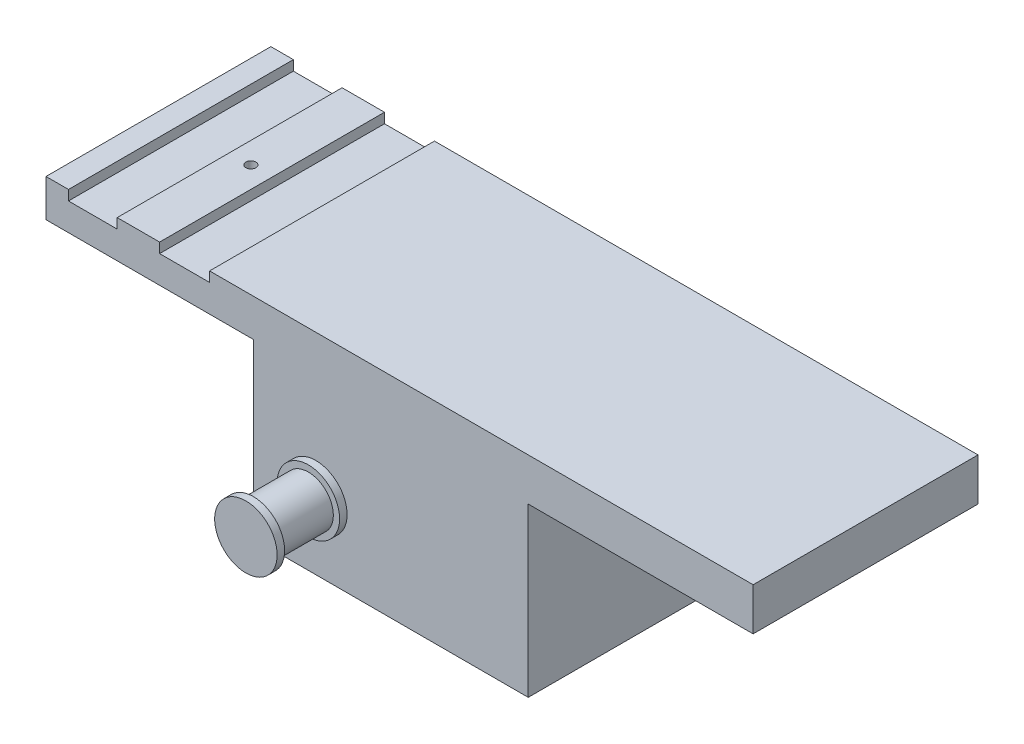
SolidWorks part; units mm, degrees
material "Alloy Steel (SS)"
ref_plane "Front Plane" through (0, 0, 0) normal (0, 0, 1) x (1, 0, 0)
ref_plane "Top Plane" through (0, 0, 0) normal (0, 1, 0) x (1, 0, 0)
ref_plane "Right Plane" through (0, 0, 0) normal (1, 0, 0) x (0, 0, -1)
sketch "Sketch1" plane through (0, 0, 0) normal (0, 0, 1) x (1, 0, 0)
  line L0 (-283, 0) -> (0, 0)
  line L1 (0, 0) -> (0, 15)
  line L2 (0, 15) -> (-217.53, 15)
  line L3 (-217.53, 15) -> (-217.53, 11)
  line L4 (-217.53, 11) -> (-237.53, 11)
  line L5 (-237.53, 11) -> (-237.53, 15)
  line L6 (-237.53, 15) -> (-254.5, 15)
  line L7 (-254.5, 15) -> (-254.5, 11)
  line L8 (-254.5, 11) -> (-274, 11)
  line L9 (-274, 11) -> (-274, 15)
  line L10 (-274, 15) -> (-283, 15)
  line L11 (-283, 15) -> (-283, 0)
  dimension "D1" = 283
  dimension "D2" = 217.53
  dimension "D3" = 9
  dimension "D4" = 19.5
  dimension "D5" = 16.97
  dimension "D6" = 20
  dimension "D7" = 15
  dimension "D8" = 4
extrude "Boss-Extrude1" add sketch "Sketch1" along normal blind 90
sketch "Sketch2" plane through (0, 15, 0) normal (0, 1, 0) x (1, 0, 0)
  line L0 (-283, -45) -> (-71.3341, -45) construction
  line L1 (-283, -90) -> (-283, 0) construction
  line L2 (-246.015, 0) -> (-246.015, -93.7366) construction
  line L3 (-237.53, 0) -> (-254.5, 0) construction
  circle A0 centre (-246.015, -45) radius 2
  dimension "D1" = 4
extrude "Cut-Extrude1" cut sketch "Sketch2" against normal blind 26
sketch "Sketch3" plane through (0, 0, 0) normal (0, 0, -1) x (-1, 0, 0)
  line L0 (213, -0.0192) -> (213, -74.1) construction
  line L1 (213, -74.1) -> (-6.6499, -74.1) construction
  line L2 (283, 0) -> (0, 0) construction
  line L3 (0, 0) -> (0, 15) construction
  line L4 (0, 0) -> (0, -61.6)
  line L5 (180, -61.6) -> (200, -61.6) construction
  line L6 (200, -61.6) -> (200, 7.5)
  line L7 (136.6106, -45.6) -> (183.3894, -45.6)
  line L8 (183.3894, -45.6) -> (191.9233, -69.0468)
  line L9 (160, -61.6) -> (160, -80.8536) construction
  line L10 (136.6106, -45.6) -> (128.0767, -69.0468)
  line L11 (140, -61.6) -> (60, -61.6) construction
  line L12 (0, -61.6) -> (200, -61.6) construction
  line L13 (100, -61.6) -> (100, 5.3066) construction
  line L14 (16.6106, -45.6) -> (8.0767, -69.0468)
  line L15 (63.3894, -45.6) -> (16.6106, -45.6)
  line L16 (63.3894, -45.6) -> (71.9233, -69.0468)
  line L17 (20, -61.6) -> (0, -61.6) construction
  line L18 (0, 0) -> (0, 7.5)
  line L19 (0, 7.5) -> (200, 7.5)
  line L20 (0, -69.0468) -> (8.0767, -69.0468)
  line L21 (200, -69.0468) -> (200, -61.6)
  line L22 (0, -61.6) -> (0, -69.0468)
  line L24 (71.9233, -69.0468) -> (128.0767, -69.0468)
  line L25 (191.9233, -69.0468) -> (200, -69.0468)
  circle A0 centre (160, -61.6) radius 10.5 construction
  circle A1 centre (160, -61.6) radius 12.5 construction
  circle A2 centre (40, -61.6) radius 10.5 construction
  circle A3 centre (40, -61.6) radius 12.5 construction
  point P21 (160, -45.6)
  dimension "D3" = 25
  dimension "D4" = 21
  dimension "D1" = 74.1
  dimension "D2" = 213
  dimension "D5" = 160
  dimension "D6" = 16
  dimension "D7" = 110
  dimension "D8" = 20
  dimension "D9" = 200
extrude "Boss-Extrude2" add sketch "Sketch3" against normal up to surface (90 mm away) up to face at (-211.0933, 11.1667, 90)
ref_plane "Plane1" through (0, 0, 44.5) normal (0, 0, -1) x (-1, 0, 0)
sketch "Sketch4" plane through (0, 0, 44.5) normal (0, 0, -1) x (-1, 0, 0)
  line L0 (16.2365, -65.0468) -> (64.159, -65.0468)
  line L1 (64.159, -65.0468) -> (64.159, -38.3472)
  line L2 (64.159, -38.3472) -> (16.2365, -38.3472)
  line L3 (16.2365, -38.3472) -> (16.2365, -65.0468)
  line L4 (0, -69.0468) -> (8.0767, -69.0468) construction
  dimension "D1" = 4
extrude "Boss-Extrude3" add sketch "Sketch4" along normal mid plane 40
sketch "Sketch6" plane through (0, 0, 0) normal (0, 0, -1) x (-1, 0, 0)
  line L0 (213, -74.1) -> (-6.6499, -74.1) construction
  line L1 (213, -74.1) -> (-6.6499, -74.1)
  circle A0 centre (160, -61.6) radius 10.5 construction
  circle A1 centre (160, -61.6) radius 12.5 construction
  circle A2 centre (40, -61.6) radius 12.5 construction
  circle A3 centre (40, -61.6) radius 10.5 construction
  circle A4 centre (160, -61.6) radius 10.5
  circle A5 centre (160, -61.6) radius 12.5
  circle A6 centre (40, -61.6) radius 12.5
  circle A7 centre (40, -61.6) radius 10.5
sketch "Sketch7" plane through (0, 0, 24.5) normal (0, 0, -1) x (-1, 0, 0)
  circle A0 centre (40, -61.6) radius 2.5
  dimension "D1" = 5
extrude "Cut-Extrude2" cut sketch "Sketch7" against normal through all
sketch "Sketch9" plane through (0, 0, 0) normal (0, 0, -1) x (-1, 0, 0)
  line L0 (160, -61.6) -> (160, -9.1635) construction
  line L1 (152.5, -40.6) -> (167.5, -40.6)
  line L2 (152.5, -40.6) -> (152.5, -32.6)
  line L3 (152.5, -32.6) -> (167.5, -32.6)
  line L4 (167.5, -40.6) -> (167.5, -32.6)
  line L5 (152.5, -40.6) -> (167.5, -32.6) construction
  line L6 (152.5, -32.6) -> (167.5, -40.6) construction
  line L7 (136.6106, -45.6) -> (183.3894, -45.6) construction
  point P0 (160, -36.6)
  dimension "D1" = 15
  dimension "D2" = 8
  dimension "D3" = 5
extrude "Cut-Extrude3" cut sketch "Sketch9" against normal through all
sketch "Sketch8" plane through (0, -45.6, 0) normal (0, -1, 0) x (1, 0, 0)
  line L0 (-136.6106, 90) -> (-183.3894, 90) construction
  line L1 (-283, 0) -> (-200, 0) construction
  line L2 (0, 90) -> (0, 0) construction
  circle A0 centre (-160, 75) radius 2.5
  circle A1 centre (-160, 15) radius 2.5
  dimension "D1" = 5
  dimension "D3" = 5
  dimension "D2" = 15
  dimension "D4" = 15
  dimension "D5" = 160
  dimension "D6" = 160
extrude "Cut-Extrude4" cut sketch "Sketch8" against normal up to next
sketch "Sketch10" plane through (0, -69.0468, 0) normal (0, -1, 0) x (1, 0, 0)
  line L1 (-8.0767, 90) -> (-90, 90)
  line L2 (-71.9233, 90) -> (-128.0767, 90) construction
  line L3 (-90, 90) -> (-90, 0)
  line L4 (-71.9233, 0) -> (-128.0767, 0) construction
  line L5 (-90, 0) -> (-8.0767, 0)
  line L6 (0, 90) -> (0, 0) construction
  line L7 (-8.0767, 0) -> (0, 0)
  line L8 (0, 0) -> (0, 90)
  line L9 (0, 90) -> (-8.0767, 90)
  dimension "D1" = 90
extrude "Cut-Extrude5" cut sketch "Sketch10" against normal blind 67
sketch "Sketch12" plane through (0, -69.0468, 0) normal (0, -1, 0) x (1, 0, 0)
  line L0 (-191.9233, 90) -> (-128.0767, 90)
  line L1 (-128.0767, 90) -> (-128.0767, 0)
  line L2 (-128.0767, 0) -> (-191.9233, 0)
  line L3 (-191.9233, 0) -> (-191.9233, 90)
extrude "Boss-Extrude4" add sketch "Sketch12" against normal blind 67
sketch "Sketch13" plane through (0, 0, 90) normal (0, 0, 1) x (1, 0, 0)
  line L0 (-90, -69.0468) -> (-200, -69.0468) construction
  line L1 (-200, -69.0468) -> (-200, 0) construction
  circle A0 centre (-175, -41.9468) radius 10
  dimension "D2" = 20
  dimension "D1" = 27.1
  dimension "D3" = 25
extrude "Boss-Extrude5" add sketch "Sketch13" along normal blind 28 and the other way blind 3
sketch "Sketch15" plane through (0, 0, 118) normal (0, 0, 1) x (1, 0, 0)
  circle A0 centre (-175, -41.9468) radius 12.5
  dimension "D1" = 25
extrude "Boss-Extrude6" add sketch "Sketch15" against normal blind 3
mirror "Mirror1" about plane through (0, 0, 44.5) normal (0, 0, -1) of "Boss-Extrude6", "Boss-Extrude5"
sketch "Sketch16" plane through (0, 0, 90) normal (0, 0, 1) x (1, 0, 0)
  circle A0 centre (-175, -41.9468) radius 12.5
  dimension "D1" = 25
extrude "Boss-Extrude7" add sketch "Sketch16" along normal blind 3
mirror "Mirror2" about plane through (0, 0, 44.5) normal (0, 0, -1) of "Boss-Extrude7"
sketch "Sketch17" plane through (0, -2.0468, 0) normal (0, -1, 0) x (-1, 0, 0)
  line L0 (0, -90) -> (90, -90) construction
  line L1 (0, 0) -> (0, -90) construction
  line L2 (74, -71) -> (0, -71) construction
  line L3 (74, -71) -> (74, -19) construction
  line L4 (74, -19) -> (0, -19) construction
  line L5 (0, -71) -> (0, -19) construction
  line L6 (74, -71) -> (0, -19) construction
  line L7 (74, -19) -> (0, -71) construction
  line L9 (54, -62) -> (20, -62)
  line L10 (54, -62) -> (54, -28)
  line L11 (54, -28) -> (20, -28)
  line L12 (20, -62) -> (20, -28)
  line L13 (54, -62) -> (20, -28) construction
  line L14 (54, -28) -> (20, -62) construction
  point P0 (37, -45)
  point P3 (37, -45)
  point P10 (37, -45)
  dimension "D4" = 34
  dimension "D1" = 45
  dimension "D2" = 74
  dimension "D3" = 52
  dimension "D5" = 34
extrude "Cut-Extrude6" cut sketch "Sketch17" against normal blind 2
sketch "Sketch18" plane through (0, -0.0468, 0) normal (0, -1, 0) x (1, 0, 0)
  line L4 (-20, 62) -> (-54, 28) construction
  circle A0 centre (-37, 45) radius 10
  dimension "D1" = 20
extrude "Cut-Extrude7" cut sketch "Sketch18" against normal blind 5
sketch "Sketch19" plane through (0, 4.9532, 0) normal (0, -1, 0) x (1, 0, 0)
  circle A0 centre (-37, 45) radius 12.5
  dimension "D1" = 25
extrude "Cut-Extrude8" cut sketch "Sketch19" against normal blind 3
